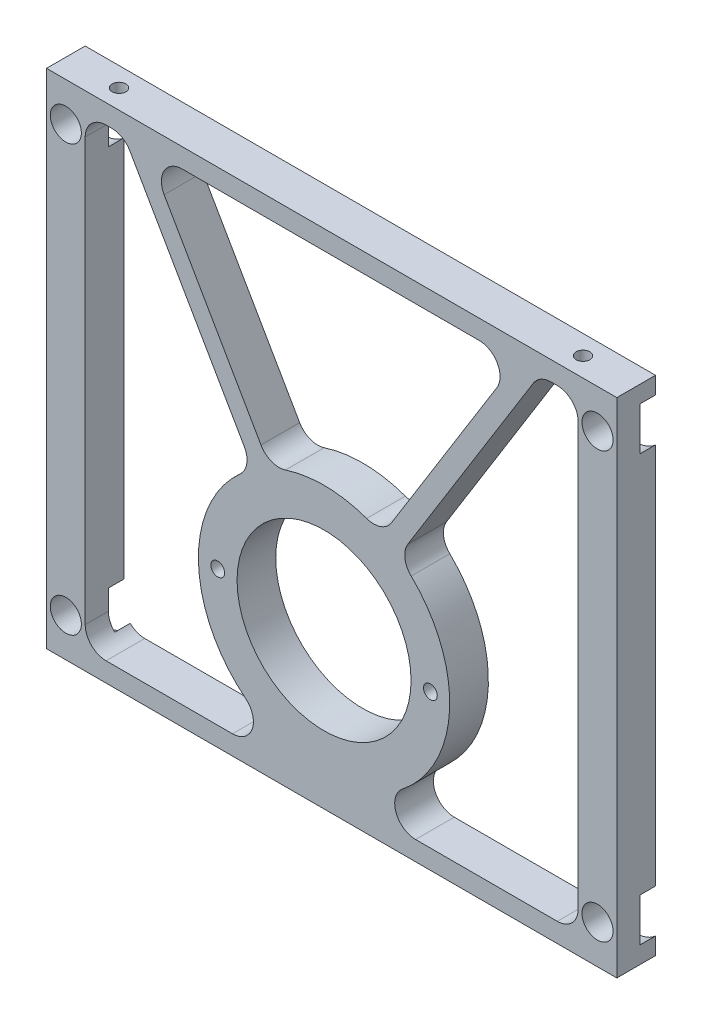
SolidWorks part; units mm, degrees
material "6061-T6 (SS)"
ref_plane "Front Plane" through (0, 0, 0) normal (0, 0, 1) x (1, 0, 0)
ref_plane "Top Plane" through (0, 0, 0) normal (0, 1, 0) x (1, 0, 0)
ref_plane "Right Plane" through (0, 0, 0) normal (1, 0, 0) x (0, 0, -1)
sketch "Sketch1" plane through (0, 0, 0) normal (0, 0, 1) x (1, 0, 0)
  line L0 (13.2944, 76.327) -> (33.6481, 76.327) construction
  line L1 (50.8, -983.6249) -> (50.8, 49016.3751) construction
  line L2 (-30.1625, -1019.5657) -> (-30.1625, 48980.4343) construction
  line L11 (-36.5125, 25.4) -> (57.15, 25.4)
  line L12 (-36.5125, 25.4) -> (-36.5125, -57.15)
  line L13 (-36.5125, -57.15) -> (57.15, -57.15)
  line L14 (57.15, 25.4) -> (57.15, -57.15)
  circle A0 centre (0, 0) radius 11.1125 construction
  circle A1 centre (9.0696, -31.75) radius 14.2875
  circle A2 centre (0, 0) radius 11.43 construction
  circle A3 centre (9.0696, -31.75) radius 21.59 construction
  circle A4 centre (9.0696, -31.75) radius 14.2875 construction
  dimension "D1" = 22.225
  dimension "D4" = 6.35
  dimension "D5" = 43.18
  dimension "D6" = 28.575
  dimension "D8" = 22.86
  dimension "D10" = 82.55
  dimension "D12" = 28.575
  dimension "D2" = 57.15
  dimension "D3" = 50.8
  dimension "D7" = 30.1625
  dimension "D9" = 25.4
  dimension "D11" = 6.35
extrude "Boss-Extrude1" add sketch "Sketch1" along normal blind 6.35
hole_wizard "#4-40 Tapped Hole2" positions "Sketch7" profile "Sketch8" tap size "#4-40" standard "ANSI Inch" end condition through all
sketch "Sketch7" plane through (0, 0, 6.35) normal (0, 0, 1) x (1, 0, 0)
  line L0 (26.5321, -31.75) -> (-8.3929, -31.75) construction
  line L2 (9.0696, -1031.75) -> (9.0696, 48968.25) construction
  circle A0 centre (9.0696, -31.75) radius 17.4625
  point P5 (-8.3929, -31.75)
  point P7 (26.5321, -31.75)
  dimension "D1" = 34.925
sketch "Sketch8" plane through (26.5321, -31.75, 6.35) normal (1, 0, 0) x (0, -1, 0)
  line L0 (0, 0) -> (0, 6.35)
  line L1 (0, 6.35) -> (1.1303, 6.35)
  line L2 (1.1303, 6.35) -> (1.1303, 0)
  line L5 (1.1303, 0) -> (0, 0)
  line L11 (0, -6.35) -> (0, 107.95) construction
  dimension "Thru Tap Drill Dia." = 2.2606
  dimension "Thru Tap Drill Depth" = 6.35
cosmetic thread "Hole Thread11" parameters "D2"=2.8448
cosmetic thread "Hole Thread12" parameters "D2"=2.8448
sketch "Sketch2" plane through (0, 0, 6.35) normal (0, 0, 1) x (1, 0, 0)
  line L0 (-30.1625, -1009.02) -> (-30.1625, 48990.98) construction
  line L1 (50.8, -1007.555) -> (50.8, 48992.445) construction
  line L2 (-36.5125, 25.4) -> (-36.5125, -57.15) construction
  line L3 (57.15, -57.15) -> (57.15, 25.4) construction
  line L4 (-20.1496, 22.225) -> (40.7128, 22.225)
  line L5 (-2.5669, -14.706) -> (-23.8125, 22.225)
  line L6 (-30.1625, -53.975) -> (-23.8125, -53.975)
  line L7 (-20.1496, 22.225) -> (0.1852, -13.1228)
  line L8 (18.5745, -13.4316) -> (40.7128, 22.225)
  line L9 (-30.1625, -53.975) -> (-30.1625, 22.225)
  line L10 (-5.9606, -53.975) -> (-23.8125, -53.975)
  line L11 (50.8, -53.975) -> (44.45, -53.975)
  line L12 (44.45, -53.975) -> (24.0998, -53.975)
  line L13 (50.8, -53.975) -> (50.8, 22.225)
  line L16 (-36.5125, -57.15) -> (57.15, -57.15) construction
  line L17 (57.15, 25.4) -> (-36.5125, 25.4) construction
  line L18 (9.0696, -29.57) -> (9.0696, -33.93) construction
  line L19 (6.6632, -31.7658) -> (11.4761, -31.7342) construction
  line L20 (-23.8125, 22.225) -> (-30.1625, 22.225)
  line L22 (21.2719, -15.1063) -> (44.45, 22.225)
  line L23 (44.45, 22.225) -> (50.8, 22.225)
  line L24 (-6.2966, -1.8556) -> (-9.0487, -3.4388) construction
  line L27 (20.4478, -10.4144) -> (23.1452, -12.0892) construction
  line L28 (-23.8125, 22.225) -> (-20.1496, 22.225) construction
  line L29 (-21.9811, 22.225) -> (9.0696, -31.75) construction
  line L30 (44.45, 22.225) -> (40.7128, 22.225) construction
  line L31 (42.5814, 22.225) -> (21.7965, -11.2518) construction
  line L32 (21.7965, -11.2518) -> (9.0696, -31.75) construction
  line L33 (-23.8125, -53.975) -> (-18.4554, -53.975) construction
  arc A1 (18.5745, -13.4316) -> (0.1852, -13.1228) centre (9.0696, -31.75) ccw
  circle A2 centre (9.0696, -31.75) radius 14.2875 construction
  arc A3 (-2.5669, -14.706) -> (-8.5958, -42.4196) centre (9.0696, -31.75) ccw
  arc A4 (27.1025, -41.786) -> (21.2719, -15.1063) centre (9.0696, -31.75) ccw
  arc A5 (-8.5958, -42.4196) -> (-3.8191, -47.8679) centre (9.0696, -31.75) ccw
  arc A9 (-5.9606, -53.975) -> (-3.8191, -47.8679) centre (-5.9606, -50.546) ccw
  arc A10 (21.9583, -47.8679) -> (24.0998, -53.975) centre (24.0998, -50.546) ccw
  arc A11 (21.9583, -47.8679) -> (27.1025, -41.786) centre (9.0696, -31.75) ccw
  point P15 (44.1583, -53.975)
  point P19 (9.0696, -31.7658)
  point P40 (9.0696, -31.75)
  dimension "D8" = 6.858
  dimension "D5" = 6.35
  dimension "D1" = 6.35
  dimension "D2" = 6.35
  dimension "D3" = 3.175
  dimension "D4" = 6.35
  dimension "D6" = 3.175
  dimension "D7" = 3.175
extrude "Cut-Extrude1" cut sketch "Sketch2" against normal through all
fillet "Fillet1" radius 3.429 12 edges at (-20.1496, 22.225, 3.175) (50.8, -53.975, 3.175) (-30.1625, -53.975, 3.175) (44.45, 22.225, 3.175) (50.8, 22.225, 3.175) (40.7128, 22.225, 3.175) (-30.1625, 22.225, 3.175) (-23.8125, 22.225, 3.175) (21.2719, -15.1063, 3.175) (18.5745, -13.4316, 3.175) (0.1852, -13.1228, 3.175) (-2.5669, -14.706, 3.175)
hole_wizard "CBORE for #10 Binding Head Machine Screw1" positions "Sketch3" profile "Sketch4" counterbore size "#10" standard "ANSI Inch" end condition through all
sketch "Sketch3" plane through (0, 0, 0) normal (0, 0, -1) x (-1, 0, 0)
  point P0 (33.3375, 19.05)
  point P3 (-53.975, 19.05)
  point P6 (-53.975, -50.8)
  point P9 (33.3375, -50.8)
sketch "Sketch4" plane through (-33.3375, 19.05, 0) normal (1, 0, 0) x (0, 1, 0)
  line L0 (0, 0) -> (0, 6.35)
  line L1 (0, 6.35) -> (2.5527, 6.35)
  line L2 (2.5527, 6.35) -> (2.5527, 2.54)
  line L3 (2.5527, 2.54) -> (4.7625, 2.54)
  line L4 (4.7625, 2.54) -> (4.7625, 0)
  line L5 (4.7625, 0) -> (0, 0)
  line L6 (0, -6.35) -> (0, 107.95) construction
  dimension "Thru Hole Dia." = 5.1054
  dimension "Thru Hole Depth" = 6.35
  dimension "C'Bore Dia." = 9.525
  dimension "C'Bore Depth" = 2.54
hole_wizard "#4-40 Tapped Hole1" positions "Sketch5" profile "Sketch6" tap size "#4-40" standard "ANSI Inch"
sketch "Sketch5" plane through (0, 25.4, 90.4875) normal (0, 1, 0) x (1, 0, 0)
  point P0 (48.4188, 87.3125)
  point P6 (-27.7812, 87.3125)
  point P9 (-27.7812, 3.175)
  point P15 (48.4188, 3.175)
sketch "Sketch6" plane through (48.4188, 25.4, 3.175) normal (1, 0, 0) x (0, 0, 1)
  line L0 (0, 0) -> (0, 10.8392)
  line L1 (0, 10.8392) -> (1.1303, 10.16)
  line L2 (1.1303, 10.16) -> (1.1303, 0)
  line L3 (1.1303, 0) -> (0, 0)
  line L4 (0, 10.8392) -> (-1.1303, 10.16) construction
  line L5 (0, -6.35) -> (0, 107.95) construction
  dimension "Tap Drill Dia." = 2.2606
  dimension "Tap Drill Depth" = 10.16
  dimension "Drill Angle" = 118
cosmetic thread "Hole Thread7" parameters "D1"=3.9556, "D2"=2.8448
cosmetic thread "Hole Thread8" parameters "D1"=3.9556, "D2"=2.8448
